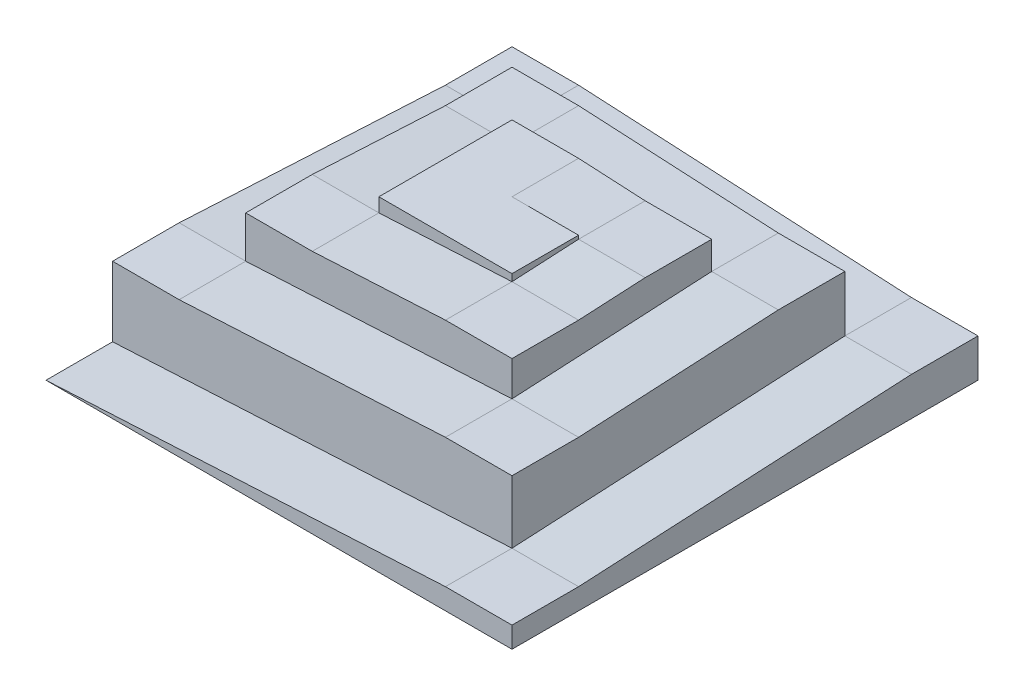
SolidWorks part; units mm, degrees
material "ABS"
ref_plane "Front Plane" through (0, 0, 0) normal (0, 0, 1) x (1, 0, 0)
ref_plane "Top Plane" through (0, 0, 0) normal (0, 1, 0) x (1, 0, 0)
ref_plane "Right Plane" through (0, 0, 0) normal (1, 0, 0) x (0, 0, -1)
sketch "Sketch1" plane through (0, 0, 0) normal (0, 0, 1) x (1, 0, 0)
  line L0 (0, 0) -> (114.3, 5.9902)
  line L2 (133.35, 0) -> (0, 0)
  line L3 (114.3, 5.9902) -> (133.35, 5.9902)
  line L4 (133.35, 5.9902) -> (133.35, 0)
  dimension "D1" = 3
  dimension "D2" = 133.35
  dimension "D3" = 19.05
extrude "Boss-Extrude1" add sketch "Sketch1" along normal blind 19.05 contours L2 L0 L3 L4
sketch "Sketch2" plane through (133.35, 0, 0) normal (1, 0, 0) x (0, 0, -1)
  line L0 (0, 0) -> (0, 5.9902)
  line L1 (0, 5.9902) -> (95.25, 10.9821)
  line L2 (95.25, 10.9821) -> (114.3, 10.9821)
  line L3 (114.3, 10.9821) -> (114.3, 0)
  line L4 (114.3, 0) -> (0, 0)
  dimension "D1" = 3
  dimension "D2" = 19.05
  dimension "D3" = 114.3
extrude "Boss-Extrude2" add sketch "Sketch2" against normal blind 19.05
sketch "Sketch3" plane through (0, 0, -114.3) normal (0, 0, -1) x (-1, 0, 0)
  line L0 (-114.3, 0) -> (-114.3, 10.9821)
  line L1 (-114.3, 10.9821) -> (-19.05, 15.9739)
  line L2 (-19.05, 15.9739) -> (0, 15.9739)
  line L3 (0, 15.9739) -> (0, 0)
  line L4 (0, 0) -> (-114.3, 0)
  dimension "D1" = 3
  dimension "D2" = 19.05
  dimension "D3" = 114.3
extrude "Boss-Extrude3" add sketch "Sketch3" against normal blind 19.05
sketch "Sketch4" plane through (0, 0, 0) normal (-1, 0, 0) x (0, 0, 1)
  line L0 (-95.25, 15.9739) -> (-19.05, 19.9674)
  line L1 (-19.05, 19.9674) -> (0, 19.9674)
  line L2 (0, 19.9674) -> (0, 0)
  line L3 (0, 0) -> (-95.25, 0)
  line L4 (-95.25, 0) -> (-95.25, 15.9739)
  dimension "D1" = 3
  dimension "D2" = 19.05
  dimension "D3" = 95.25
extrude "Boss-Extrude4" add sketch "Sketch4" against normal blind 19.05
sketch "Sketch5" plane through (0, 0, 0) normal (0, 0, 1) x (1, 0, 0)
  line L0 (95.25, 23.9608) -> (19.05, 19.9674)
  line L1 (19.05, 19.9674) -> (19.05, 0)
  line L2 (19.05, 0.9984) -> (19.05, 19.9674) construction
  line L3 (19.05, 0) -> (114.3, 0)
  line L4 (114.3, 0) -> (114.3, 23.9608)
  line L5 (114.3, 23.9608) -> (95.25, 23.9608)
  dimension "D1" = 19.05
  dimension "D2" = 3
  dimension "D3" = 95.25
extrude "Boss-Extrude5" add sketch "Sketch5" against normal blind 19.05
sketch "Sketch6" plane through (114.3, 0, 0) normal (1, 0, 0) x (0, 0, -1)
  line L0 (19.05, 23.9608) -> (76.2, 26.9559)
  line L1 (76.2, 26.9559) -> (95.25, 26.9559)
  line L2 (95.25, 26.9559) -> (95.25, 0)
  line L3 (95.25, 0) -> (19.05, 0)
  line L4 (19.05, 0) -> (19.05, 23.9608)
  dimension "D1" = 3
  dimension "D2" = 19.05
  dimension "D3" = 76.2
extrude "Boss-Extrude6" add sketch "Sketch6" against normal blind 19.05
sketch "Sketch7" plane through (0, 0, -95.25) normal (0, 0, -1) x (-1, 0, 0)
  line L0 (-95.25, 26.9559) -> (-38.1, 29.951)
  line L1 (-38.1, 29.951) -> (-19.05, 29.951)
  line L2 (-19.05, 29.951) -> (-19.05, 0)
  line L3 (-19.05, 0) -> (-95.25, 0)
  line L4 (-95.25, 0) -> (-95.25, 26.9559)
  dimension "D1" = 3
  dimension "D2" = 19.05
  dimension "D3" = 76.2
extrude "Boss-Extrude7" add sketch "Sketch7" against normal blind 19.05
sketch "Sketch8" plane through (19.05, 0, 0) normal (-1, 0, 0) x (0, 0, 1)
  line L0 (-76.2, 29.951) -> (-38.1, 31.9478)
  line L1 (-38.1, 31.9478) -> (-19.05, 31.9478)
  line L2 (-19.05, 31.9478) -> (-19.05, 0)
  line L3 (-19.05, 0) -> (-76.2, 0)
  line L4 (-76.2, 16.9723) -> (-76.2, 29.951) construction
  line L5 (-76.2, 0) -> (-76.2, 29.951)
  dimension "D1" = 3
  dimension "D2" = 19.05
  dimension "D3" = 57.15
extrude "Boss-Extrude8" add sketch "Sketch8" against normal blind 19.05 contours L3 L5 L0 L1 L2
sketch "Sketch9" plane through (0, 0, -19.05) normal (0, 0, 1) x (1, 0, 0)
  line L0 (38.1, 31.9478) -> (76.2, 33.9445)
  line L1 (76.2, 33.9445) -> (95.25, 33.9445)
  line L2 (95.25, 33.9445) -> (95.25, 0)
  line L3 (95.25, 0) -> (38.1, 0)
  line L4 (38.1, 0) -> (38.1, 31.9478)
  dimension "D1" = 3
  dimension "D2" = 19.05
  dimension "D3" = 57.15
extrude "Boss-Extrude9" add sketch "Sketch9" against normal blind 19.05
sketch "Sketch10" plane through (95.25, 0, 0) normal (1, 0, 0) x (0, 0, -1)
  line L0 (38.1, 0) -> (38.1, 33.9445)
  line L1 (38.1, 33.9445) -> (57.15, 34.9429)
  line L2 (57.15, 34.9429) -> (76.2, 34.9429)
  line L3 (76.2, 34.9429) -> (76.2, 0)
  line L4 (76.2, 0) -> (38.1, 0)
  dimension "D1" = 3
  dimension "D2" = 38.1
  dimension "D3" = 19.05
extrude "Boss-Extrude10" add sketch "Sketch10" against normal blind 19.05
sketch "Sketch11" plane through (0, 0, -76.2) normal (0, 0, -1) x (-1, 0, 0)
  line L0 (-76.2, 34.9429) -> (-57.15, 35.9413)
  line L1 (-57.15, 35.9413) -> (-38.1, 35.9413)
  line L2 (-38.1, 35.9413) -> (-38.1, 0)
  line L3 (-38.1, 0) -> (-76.2, 0)
  line L4 (-76.2, 0) -> (-76.2, 34.9429)
  dimension "D1" = 3
  dimension "D2" = 19.05
  dimension "D3" = 38.1
extrude "Boss-Extrude11" add sketch "Sketch11" against normal blind 19.05
sketch "Sketch12" plane through (0, 0, -57.15) normal (0, 0, 1) x (1, 0, 0)
  line L0 (38.1, 35.9413) -> (76.2, 35.9413)
  line L1 (76.2, 35.9413) -> (76.2, 0)
  line L2 (76.2, 0) -> (38.1, 0)
  line L3 (38.1, 0) -> (38.1, 35.9413)
  dimension "D1" = 38.1
extrude "Boss-Extrude12" add sketch "Sketch12" along normal blind 19.05
